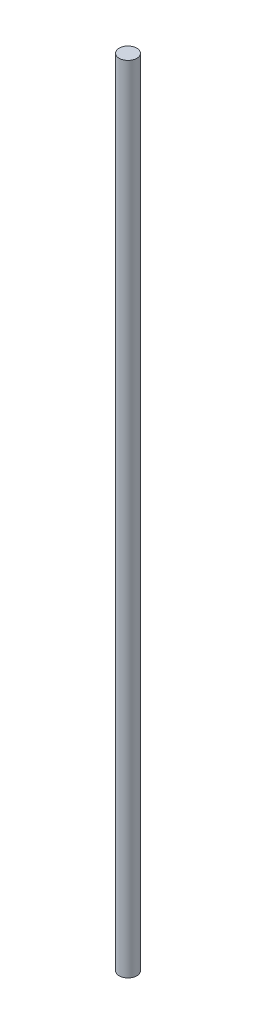
SolidWorks part; units mm, degrees
material "6061 Alloy"
ref_plane "Front Plane" through (0, 0, 0) normal (0, 0, 1) x (1, 0, 0)
ref_plane "Top Plane" through (0, 0, 0) normal (0, 1, 0) x (1, 0, 0)
ref_plane "Right Plane" through (0, 0, 0) normal (1, 0, 0) x (0, 0, -1)
sketch "Sketch1" plane through (0, 0, 0) normal (0, 1, 0) x (1, 0, 0)
  circle A0 centre (0, 0) radius 6.35
  dimension "D1" = 12.7
extrude "Boss-Extrude1" add sketch "Sketch1" along normal blind 571.5
